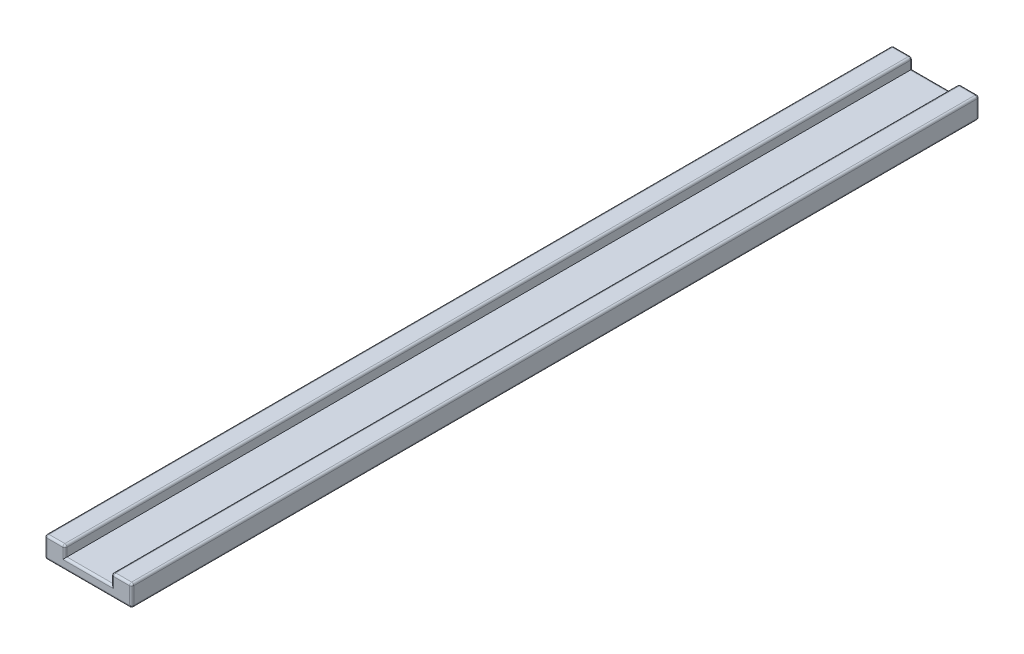
SolidWorks part; units mm, degrees
ref_plane "Front Plane" through (0, 0, 0) normal (0, 0, 1) x (1, 0, 0)
ref_plane "Top Plane" through (0, 0, 0) normal (0, 1, 0) x (1, 0, 0)
ref_plane "Right Plane" through (0, 0, 0) normal (1, 0, 0) x (0, 0, -1)
sketch "Sketch1" plane through (0, 0, 0) normal (0, 0, 1) x (1, 0, 0)
  line L0 (-11, 5) -> (-11, 0)
  line L1 (-20.5, -5) -> (20.5, -5)
  line L2 (-20.5, -5) -> (-20.5, 5)
  line L3 (-20.5, 5) -> (-11, 5)
  line L4 (20.5, -5) -> (20.5, 5)
  line L5 (-20.5, -5) -> (20.5, 5) construction
  line L6 (-20.5, 5) -> (20.5, -5) construction
  line L7 (-11, 0) -> (11, 0)
  line L8 (11, 0) -> (11, 5)
  line L9 (11, 5) -> (20.5, 5)
  point P0 (0, 0)
  dimension "D1" = 41
  dimension "D2" = 10
  dimension "D3" = 22
  dimension "D4" = 9.5
extrude "Boss-Extrude1" add sketch "Sketch1" along normal blind 400
ref_plane "Plane1" through (0, 0, 200) normal (0, 0, -1) x (-1, 0, 0)
fillet "Fillet1" radius 1 6 edges at (11, 5, 200) (-11, 5, 200) (20.5, -5, 200) (-20.5, -5, 200) (-20.5, 5, 200) (20.5, 5, 200)
fillet "Fillet2" radius 1 28 edges at (0, 0, 0) (-11, 2, 0) (-11.2929, 4.7071, 0) (-15.75, 5, 0) (-20.2071, 4.7071, 0) (-20.5, 0, 0) (-20.2071, -4.7071, 0) (0, -5, 0) (20.2071, -4.7071, 0) (20.5, 0, 0) (20.2071, 4.7071, 0) (15.75, 5, 0) (11.2929, 4.7071, 0) (11, 2, 0) (20.2071, 4.7071, 400) (20.5, 0, 400) (20.2071, -4.7071, 400) (0, -5, 400) (-20.2071, -4.7071, 400) (-20.5, 0, 400) (-20.2071, 4.7071, 400) (-15.75, 5, 400) (-11.2929, 4.7071, 400) (-11, 2, 400) (0, 0, 400) (11, 2, 400) (11.2929, 4.7071, 400) (15.75, 5, 400)
sketch "Sketch2" plane through (0, -5, 0) normal (0, -1, 0) x (1, 0, 0)
  line L0 (-19.5, 1) -> (19.5, 1) construction
  point P0 (0, 31)
  point P1 (0, 71)
  point P2 (0, 51)
  dimension "D1" = 30
  dimension "D2" = 50
  dimension "D3" = 70
